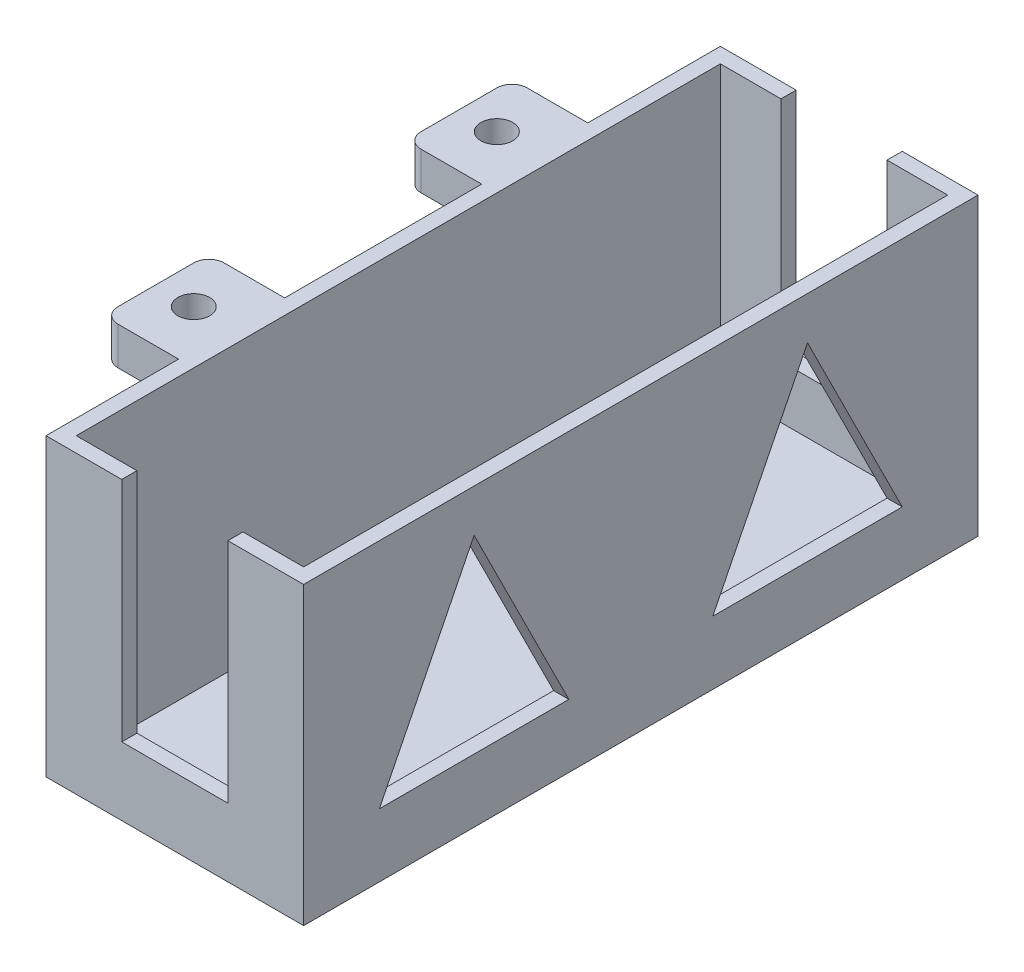
SolidWorks part; units mm, degrees
ref_plane "Front Plane" through (0, 0, 0) normal (0, 0, 1) x (1, 0, 0)
ref_plane "Top Plane" through (0, 0, 0) normal (0, 1, 0) x (1, 0, 0)
ref_plane "Right Plane" through (0, 0, 0) normal (1, 0, 0) x (0, 0, -1)
sketch "Sketch1" plane through (0, 0, 0) normal (0, 1, 0) x (1, 0, 0)
  line L1 (109.4484, -179.3604) -> (119.4484, -179.3604)
  line L2 (109.4484, -179.3604) -> (109.4484, -165.3604)
  line L3 (109.4484, -165.3604) -> (119.4484, -165.3604)
  line L4 (119.4484, -179.3604) -> (119.4484, -165.3604)
  line L5 (109.4484, -179.3604) -> (119.4484, -165.3604) construction
  line L6 (109.4484, -165.3604) -> (119.4484, -179.3604) construction
  line L8 (109.4484, -125.3604) -> (119.4484, -125.3604)
  line L9 (109.4484, -125.3604) -> (109.4484, -139.3604)
  line L10 (109.4484, -139.3604) -> (119.4484, -139.3604)
  line L11 (119.4484, -125.3604) -> (119.4484, -139.3604)
  line L12 (109.4484, -125.3604) -> (119.4484, -139.3604) construction
  line L13 (109.4484, -139.3604) -> (119.4484, -125.3604) construction
  circle A0 centre (114.4484, -172.3604) radius 2.1
  circle A1 centre (114.4484, -132.3604) radius 2.1
  point P0 (114.4484, -172.3604)
  point P8 (114.4484, -132.3604)
  dimension "D1" = 7
  dimension "D2" = 14
sketch "Sketch2" plane through (0, 0, 0) normal (0, 1, 0) x (1, 0, 0)
  line L1 (109.4484, -125.3604) -> (119.4484, -125.3604)
  line L2 (109.4484, -125.3604) -> (109.4484, -139.3604)
  line L3 (109.4484, -139.3604) -> (119.4484, -139.3604)
  line L4 (119.4484, -125.3604) -> (119.4484, -139.3604)
  line L5 (109.4484, -165.3604) -> (119.4484, -165.3604)
  line L6 (109.4484, -165.3604) -> (109.4484, -179.3604)
  line L7 (109.4484, -179.3604) -> (119.4484, -179.3604)
  line L8 (119.4484, -165.3604) -> (119.4484, -179.3604)
  circle A0 centre (114.4484, -132.3604) radius 2.1
  circle A1 centre (114.4484, -172.3604) radius 2.1
extrude "Boss-Extrude1" add sketch "Sketch2" along normal blind 5 contours L6 L5 L8 L7 | L2 L1 L4 L3 | A1 | A0
sketch "Sketch3" plane through (119.4484, 0, 0) normal (1, 0, 0) x (0, 0, -1)
  line L0 (-179.3604, 5) -> (-125.3604, 5) construction
  line L1 (-107.8604, 5) -> (-107.8604, -34)
  line L2 (-107.8604, 5) -> (-196.8604, 5)
  line L3 (-152.3604, 5) -> (-152.3604, -34)
  line L4 (-107.8604, -34) -> (-196.8604, -34)
  line L5 (-196.8604, 5) -> (-196.8604, -34)
  line M6 (-179.3604, 0) -> (-165.3604, 0)
  line M7 (-165.3604, 0) -> (-165.3604, 5)
  line M8 (-165.3604, 5) -> (-179.3604, 5)
  line M9 (-179.3604, 5) -> (-179.3604, 0)
  dimension "D1" = 39
  dimension "D2" = 44.5
extrude "Boss-Extrude2" add sketch "Sketch3" along normal blind 2 contours L2 L5 L4 L3 M7 M6 M9 | L4 L1 L2 L3 | M9 M6 M7 M8
sketch "Sketch4" plane through (121.4484, 0, 0) normal (1, 0, 0) x (0, 0, -1)
  line L0 (-107.8604, -34) -> (-196.8604, -34) construction
  line L1 (-196.8604, 5) -> (-194.8604, 5)
  line L2 (-196.8604, 5) -> (-196.8604, -34)
  line L3 (-196.8604, -34) -> (-194.8604, -34)
  line L4 (-194.8604, 5) -> (-194.8604, -34)
  line L5 (-152.3604, 5) -> (-152.3604, -34) construction
  line L6 (-107.8604, 5) -> (-196.8604, 5) construction
  line L7 (-107.8604, -34) -> (-109.8604, -34)
  line L8 (-109.8604, 5) -> (-109.8604, -34)
  line L9 (-107.8604, 5) -> (-109.8604, 5)
  line L10 (-107.8604, 5) -> (-107.8604, -34)
  line L13 (-194.8604, 5) -> (-194.8604, 3)
  line L15 (-109.8604, 5) -> (-109.8604, 3)
  line L16 (-194.8604, -34) -> (-109.8604, -34)
  line L17 (-194.8604, -34) -> (-194.8604, -32)
  line L18 (-194.8604, -32) -> (-109.8604, -32)
  line L19 (-109.8604, -34) -> (-109.8604, -32)
  line M6 (-107.8604, -34) -> (-107.8604, 5)
  line M7 (-107.8604, 5) -> (-196.8604, 5)
  line M8 (-196.8604, 5) -> (-196.8604, -34)
  line M9 (-196.8604, -34) -> (-107.8604, -34)
  dimension "D1" = 2
  dimension "D2" = 2
  dimension "D3" = 2
extrude "Boss-Extrude4" add sketch "Sketch4" along normal blind 32 contours L5 L18 L4 M9 | L18 L5 L16 L8 | L8 M7 M9 M6 | L4 M7 M8 M9
sketch "Sketch5" plane through (0, -32, 0) normal (0, 1, 0) x (1, 0, 0)
  line L0 (153.4484, -194.8604) -> (121.4484, -194.8604) construction
  line L1 (153.4484, -109.8604) -> (151.4484, -109.8604)
  line L2 (153.4484, -109.8604) -> (153.4484, -194.8604)
  line L3 (153.4484, -194.8604) -> (151.4484, -194.8604)
  line L4 (151.4484, -109.8604) -> (151.4484, -194.8604)
  dimension "D1" = 2
extrude "Boss-Extrude5" add sketch "Sketch5" along normal up to surface (37 mm away) up to face at (125.6984, 5, 152.3604)
sketch "Sketch6" plane through (0, 0, 196.8604) normal (0, 0, 1) x (1, 0, 0)
  line L0 (153.4484, 5) -> (119.4484, 5) construction
  line L1 (129.4484, 5) -> (143.4484, 5)
  line L2 (129.4484, 5) -> (129.4484, -25)
  line L3 (129.4484, -25) -> (143.4484, -25)
  line L4 (143.4484, 5) -> (143.4484, -25)
  line L5 (153.4484, 5) -> (153.4484, -34) construction
  line L6 (119.4484, 5) -> (119.4484, -34) construction
  dimension "D1" = 10
  dimension "D2" = 10
  dimension "D3" = 30
extrude "Cut-Extrude1" cut sketch "Sketch6" against normal blind 200
sketch "Sketch7" plane through (153.4484, 0, 0) normal (1, 0, 0) x (0, 0, -1)
  line L0 (-196.8604, -14.5) -> (-107.8604, -14.5) construction
  line L1 (-196.8604, 5) -> (-196.8604, -34) construction
  line L2 (-107.8604, -34) -> (-107.8604, 5) construction
  line L4 (-189.3604, -24.5) -> (-169.3604, -24.5)
  line L5 (-189.3604, -24.5) -> (-189.3604, -4.5)
  line L6 (-189.3604, -4.5) -> (-169.3604, -4.5)
  line L7 (-169.3604, -24.5) -> (-169.3604, -4.5)
  line L8 (-189.3604, -24.5) -> (-169.3604, -4.5) construction
  line L9 (-189.3604, -4.5) -> (-169.3604, -24.5) construction
  line L10 (-162.3604, -24.5) -> (-142.3604, -24.5)
  line L11 (-162.3604, -24.5) -> (-162.3604, -4.5)
  line L12 (-162.3604, -4.5) -> (-142.3604, -4.5)
  line L13 (-142.3604, -24.5) -> (-142.3604, -4.5)
  line L14 (-162.3604, -24.5) -> (-142.3604, -4.5) construction
  line L15 (-162.3604, -4.5) -> (-142.3604, -24.5) construction
  line L16 (-135.3604, -24.5) -> (-115.3604, -24.5)
  line L17 (-135.3604, -24.5) -> (-135.3604, -4.5)
  line L18 (-135.3604, -4.5) -> (-115.3604, -4.5)
  line L19 (-115.3604, -24.5) -> (-115.3604, -4.5)
  line L20 (-135.3604, -24.5) -> (-115.3604, -4.5) construction
  line L21 (-135.3604, -4.5) -> (-115.3604, -24.5) construction
  point P6 (-179.3604, -14.5)
  point P11 (-152.3604, -14.5)
  point P16 (-125.3604, -14.5)
  dimension "D1" = 7
  dimension "D2" = 20
  dimension "D3" = 20
  dimension "D4" = 20
  dimension "D5" = 20
  dimension "D6" = 20
  dimension "D7" = 20
  dimension "D8" = 7.5
extrude "Cut-Extrude2" cut sketch "Sketch7" against normal blind 16
fillet "Fillet1" radius 2 4 edges at (109.4484, 2.5, 125.3604) (109.4484, 2.5, 139.3604) (109.4484, 2.5, 165.3604) (109.4484, 2.5, 179.3604)
sketch "Sketch8" plane through (153.4484, 0, 0) normal (1, 0, 0) x (0, 0, -1)
  line L1 (-208.3883, 12.4688) -> (-88.7688, 12.4688)
  line L2 (-208.3883, 12.4688) -> (-208.3883, -43.1388)
  line L3 (-208.3883, -43.1388) -> (-88.7688, -43.1388)
  line L4 (-88.7688, 12.4688) -> (-88.7688, -43.1388)
extrude "Cut-Extrude3" cut sketch "Sketch8" against normal up to surface (32 mm away) up to face at (121.4484, -13.5, 152.3604)
sketch "Sketch9" plane through (121.4484, 0, 0) normal (1, 0, 0) x (0, 0, -1)
  line L0 (-152.3604, 5) -> (-152.3604, -34) construction
  line L1 (-107.8604, 5) -> (-196.8604, 5) construction
  line L2 (-107.8604, -34) -> (-196.8604, -34) construction
  line L3 (-102.3604, 5) -> (-102.3604, -30)
  line L4 (-102.3604, 5) -> (-202.3604, 5)
  line L5 (-152.3604, 5) -> (-152.3604, -30)
  line L6 (-102.3604, -30) -> (-202.3604, -30)
  line L7 (-202.3604, 5) -> (-202.3604, -30)
  line M7 (-107.8604, -34) -> (-107.8604, 5)
  line M9 (-196.8604, 5) -> (-196.8604, -34)
  line M10 (-196.8604, -34) -> (-107.8604, -34)
  dimension "D1" = 50
  dimension "D2" = 35
extrude "Boss-Extrude6" add sketch "Sketch9" against normal up to surface (2 mm away) contours L4 L7 L6 M9 | L6 L3 L4 M7 | L6 L5 L4 M9 | L0 L6 M9 M10 | L6 L0 M10 M7 up to face at (119.4484, -3.1667, 152.3604)
sketch "Sketch10" plane through (121.4484, 0, 0) normal (1, 0, 0) x (0, 0, -1)
  line L1 (-196.8604, -30) -> (-107.8604, -30)
  line L2 (-196.8604, -30) -> (-196.8604, -34)
  line L3 (-196.8604, -34) -> (-107.8604, -34)
  line L4 (-107.8604, -30) -> (-107.8604, -34)
extrude "Cut-Extrude4" cut sketch "Sketch10" against normal blind 10
sketch "Sketch11" plane through (121.4484, 0, 0) normal (1, 0, 0) x (0, 0, -1)
  line L1 (-202.3604, 5) -> (-204.3604, 5)
  line L2 (-202.3604, 5) -> (-202.3604, -30)
  line L3 (-202.3604, -30) -> (-204.3604, -30)
  line L4 (-204.3604, 5) -> (-204.3604, -30)
  line L5 (-102.3604, 5) -> (-100.3604, 5)
  line L6 (-102.3604, 5) -> (-102.3604, -30)
  line L7 (-102.3604, -30) -> (-100.3604, -30)
  line L8 (-100.3604, 5) -> (-100.3604, -30)
  line L9 (-204.3604, -30) -> (-100.3604, -30)
  line L10 (-204.3604, -30) -> (-204.3604, -32)
  line L11 (-204.3604, -32) -> (-100.3604, -32)
  line L12 (-100.3604, -30) -> (-100.3604, -32)
  line M4 (-202.3604, 5) -> (-202.3604, -30)
  line M5 (-202.3604, -30) -> (-102.3604, -30)
  dimension "D1" = 2
  dimension "D2" = 2
  dimension "D3" = 2
extrude "Boss-Extrude7" add sketch "Sketch11" along normal blind 25 separate body contours L1 L4 L3 M4 | L12 L7 L3 L10 L11 M5
sketch "Sketch12" plane through (121.4484, 0, 0) normal (-1, 0, 0) x (0, 0, 1)
  line L0 (204.3604, 5) -> (204.3604, -32) construction
  line L1 (100.3604, 5) -> (102.3604, 5)
  line L2 (100.3604, 5) -> (100.3604, -30)
  line L3 (100.3604, -30) -> (102.3604, -30)
  line L4 (102.3604, 5) -> (102.3604, -30)
  line L5 (202.3604, 5) -> (204.3604, 5)
  line L6 (202.3604, 5) -> (202.3604, -30)
  line L7 (202.3604, -30) -> (204.3604, -30)
  line L8 (204.3604, 5) -> (204.3604, -30)
  line L10 (204.3604, -32) -> (100.3604, -32)
  line L11 (204.3604, -32) -> (204.3604, -30)
  line L12 (204.3604, -30) -> (100.3604, -30)
  line L13 (100.3604, -32) -> (100.3604, -30)
  line M1 (204.3604, 5) -> (202.3604, 5)
  line M2 (202.3604, 5) -> (202.3604, -30)
  line M3 (202.3604, -30) -> (102.3604, -30)
  line M4 (102.3604, -30) -> (102.3604, 5)
  line M5 (102.3604, 5) -> (100.3604, 5)
  line M6 (100.3604, 5) -> (100.3604, -32)
  line M7 (100.3604, -32) -> (204.3604, -32)
  line M8 (204.3604, -32) -> (204.3604, 5)
extrude "Boss-Extrude8" add sketch "Sketch12" along normal blind 2 contours L3 M6 M4 M5 | L7 L3 M3 M6 M7 M8 | L7 M2 M8 M1
sketch "Sketch13" plane through (146.4484, 0, 0) normal (1, 0, 0) x (0, 0, -1)
  line L0 (-204.3604, -22) -> (-100.3604, -22) construction
  line L1 (-204.3604, 5) -> (-100.3604, 5)
  line L2 (-204.3604, 5) -> (-204.3604, -32)
  line L3 (-204.3604, -32) -> (-100.3604, -32)
  line L4 (-100.3604, 5) -> (-100.3604, -32)
  line L5 (-195.7981, -22) -> (-175.7981, -22)
  line L6 (-175.7981, -22) -> (-185.7981, -0.5549)
  line L7 (-185.7981, -0.5549) -> (-195.7981, -22)
  line L8 (-152.3604, 5) -> (-152.3604, -32) construction
  line L9 (-128.9227, -22) -> (-118.9227, -0.5549)
  line L10 (-108.9227, -22) -> (-128.9227, -22)
  line L11 (-118.9227, -0.5549) -> (-108.9227, -22)
  line L12 (-162.3604, -22) -> (-142.3604, -22)
  line L13 (-118.9227, -0.5549) -> (-152.3604, -0.5549) construction
  line L14 (-142.3604, -22) -> (-152.3604, -0.5549)
  line L15 (-162.3604, -22) -> (-152.3604, -0.5549)
  point P19 (-152.3604, -22)
  dimension "D1" = 10
  dimension "D2" = 20
  dimension "D3" = 10
  dimension "D4" = 115
  dimension "D5" = 20
extrude "Boss-Extrude9" add sketch "Sketch13" along normal blind 2 contours L2 L1 L4 L3 | L9 L11 L10 | L15 L14 L12 | L7 L5 L6
sketch "Sketch14" plane through (0, 0, 100.3604) normal (0, 0, -1) x (-1, 0, 0)
  line L0 (-133.9484, 5) -> (-133.9484, -32) construction
  line L1 (-119.4484, 5) -> (-148.4484, 5) construction
  line L2 (-119.4484, -32) -> (-148.4484, -32) construction
  line L4 (-140.4484, -10) -> (-127.4484, -10)
  line L5 (-140.4484, -10) -> (-140.4484, 20)
  line L6 (-140.4484, 20) -> (-127.4484, 20)
  line L7 (-127.4484, -10) -> (-127.4484, 20)
  line L8 (-140.4484, -10) -> (-127.4484, 20) construction
  line L9 (-140.4484, 20) -> (-127.4484, -10) construction
  dimension "D1" = 30
  dimension "D2" = 13
extrude "Cut-Extrude5" cut sketch "Sketch14" against normal up to surface (104 mm away) up to face at (133.9484, -13.5, 204.3604)
sketch "Sketch15" plane through (148.4484, 0, 0) normal (1, 0, 0) x (0, 0, -1)
  line L1 (-209.1927, -39.1221) -> (-95.3008, -39.1221)
  line L2 (-209.1927, -39.1221) -> (-209.1927, 12.4816)
  line L3 (-209.1927, 12.4816) -> (-95.3008, 12.4816)
  line L4 (-95.3008, -39.1221) -> (-95.3008, 12.4816)
  line L5 (-209.1927, -39.1221) -> (-95.3008, 12.4816) construction
  line L6 (-209.1927, 12.4816) -> (-95.3008, -39.1221) construction
  point P0 (-152.2468, -13.3202)
extrude "Cut-Extrude6" cut sketch "Sketch15" against normal up to surface (27 mm away) up to face at (121.4484, -12.5, 152.3604)
sketch "Sketch16" plane through (121.4484, 0, 0) normal (1, 0, 0) x (0, 0, -1)
  line L1 (-208.9653, 10.563) -> (-94.7325, 10.563)
  line L2 (-208.9653, 10.563) -> (-208.9653, -39.222)
  line L3 (-208.9653, -39.222) -> (-94.7325, -39.222)
  line L4 (-94.7325, 10.563) -> (-94.7325, -39.222)
extrude "Cut-Extrude7" cut sketch "Sketch16" against normal up to surface (2 mm away) up to face at (119.4484, -2.8333, 152.3604)
sketch "Sketch17" plane through (119.4484, 0, 0) normal (1, 0, 0) x (0, 0, -1)
  line L0 (-179.3604, 5) -> (-125.3604, 5) construction
  line L1 (-107.8604, 5) -> (-107.8604, -34)
  line L2 (-107.8604, 5) -> (-196.8604, 5)
  line L4 (-107.8604, -34) -> (-196.8604, -34)
  line L5 (-196.8604, 5) -> (-196.8604, -34)
  dimension "D1" = 39
extrude "Boss-Extrude10" add sketch "Sketch17" along normal blind 34
sketch "Sketch18" plane through (0, 5, 0) normal (0, 1, 0) x (1, 0, 0)
  line L0 (153.4484, -107.8604) -> (153.4484, -196.8604) construction
  line L1 (121.4484, -109.8604) -> (151.4484, -109.8604)
  line L2 (121.4484, -109.8604) -> (121.4484, -194.8604)
  line L3 (121.4484, -194.8604) -> (151.4484, -194.8604)
  line L4 (151.4484, -109.8604) -> (151.4484, -194.8604)
  line L5 (119.4484, -107.8604) -> (119.4484, -125.3604) construction
  line L6 (153.4484, -196.8604) -> (119.4484, -196.8604) construction
  line L7 (153.4484, -107.8604) -> (119.4484, -107.8604) construction
  dimension "D1" = 2
  dimension "D2" = 2
  dimension "D3" = 2
  dimension "D4" = 2
extrude "Cut-Extrude8" cut sketch "Sketch18" against normal blind 37
sketch "Sketch19" plane through (0, 0, 196.8604) normal (0, 0, 1) x (1, 0, 0)
  line L0 (136.4484, 5) -> (136.4484, -34) construction
  line L1 (153.4484, 5) -> (119.4484, 5) construction
  line L2 (153.4484, -34) -> (119.4484, -34) construction
  line L3 (143.4484, 5) -> (143.4484, -25)
  line L4 (143.4484, 5) -> (129.4484, 5)
  line L5 (136.4484, 5) -> (136.4484, -25)
  line L6 (143.4484, -25) -> (129.4484, -25)
  line L7 (129.4484, 5) -> (129.4484, -25)
  line M9 (153.4484, 5) -> (119.4484, 5)
  dimension "D1" = 7
  dimension "D2" = 30
extrude "Cut-Extrude9" cut sketch "Sketch19" against normal blind 93 contours L4 L7 L6 L5 | L6 L3 L5 M9
sketch "Sketch20" plane through (153.4484, 0, 0) normal (1, 0, 0) x (0, 0, -1)
  line L0 (-186.8604, -25.6375) -> (-161.8604, -25.6375)
  line L1 (-174.3604, -25.6375) -> (-174.3604, -0.6375) construction
  line L2 (-174.3604, -0.6375) -> (-186.8604, -25.6375)
  line L3 (-161.8604, -25.6375) -> (-174.3604, -0.6375)
  line L4 (-196.8604, 5) -> (-196.8604, -34) construction
  line L5 (-152.3604, 5) -> (-152.3604, -34) construction
  line L6 (-107.8604, 5) -> (-196.8604, 5) construction
  line L7 (-196.8604, -34) -> (-107.8604, -34) construction
  line L8 (-117.8604, -25.6375) -> (-142.8604, -25.6375)
  line L9 (-130.3604, -0.6375) -> (-117.8604, -25.6375)
  line L10 (-142.8604, -25.6375) -> (-130.3604, -0.6375)
  dimension "D1" = 25
  dimension "D2" = 25
  dimension "D3" = 10
extrude "Cut-Extrude10" cut sketch "Sketch20" against normal blind 17
